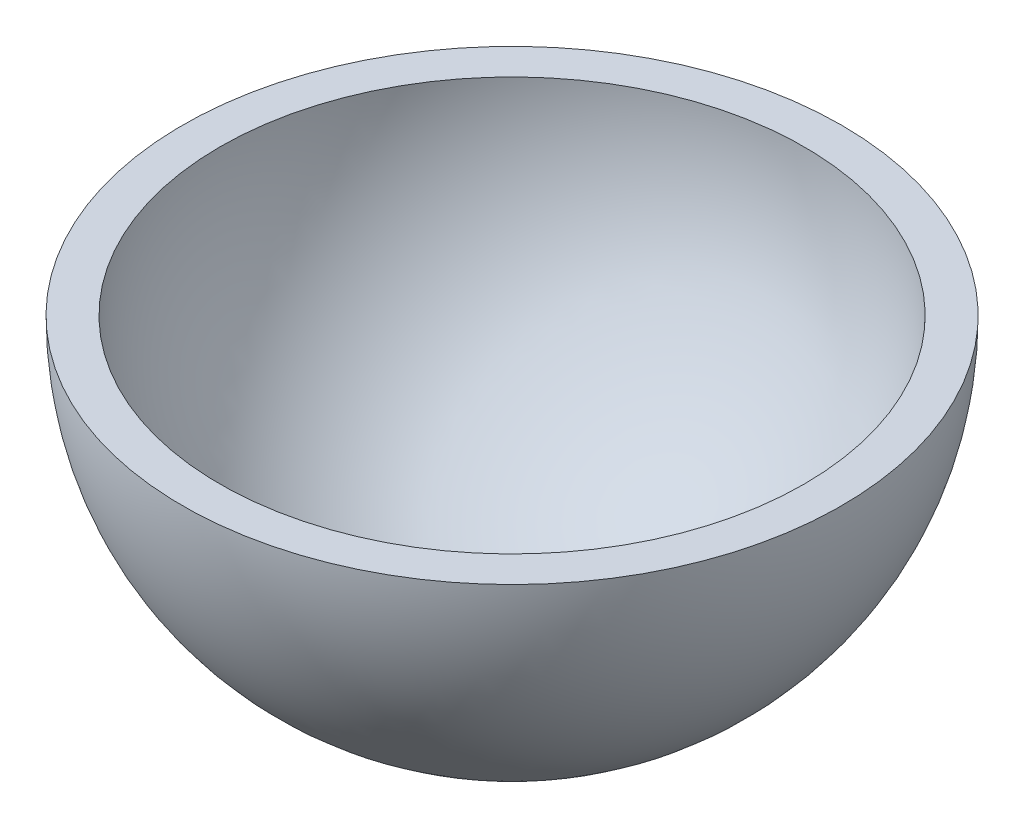
SolidWorks part; units mm, degrees
ref_plane "Front Plane" through (0, 0, 0) normal (0, 0, 1) x (1, 0, 0)
ref_plane "Top Plane" through (0, 0, 0) normal (0, 1, 0) x (1, 0, 0)
ref_plane "Right Plane" through (0, 0, 0) normal (1, 0, 0) x (0, 0, -1)
sketch "Sketch1" plane through (0, 0, 0) normal (0, 1, 0) x (1, 0, 0)
  line L0 (0, 0) -> (0, 22)
  arc A0 (0, 22) -> (0, 0) centre (0, 11) cw
  dimension "D1" = 22
revolve "Revolve1" add sketch "Sketch1" angle 180 about L0
shell "Shell1" thickness 1.25
